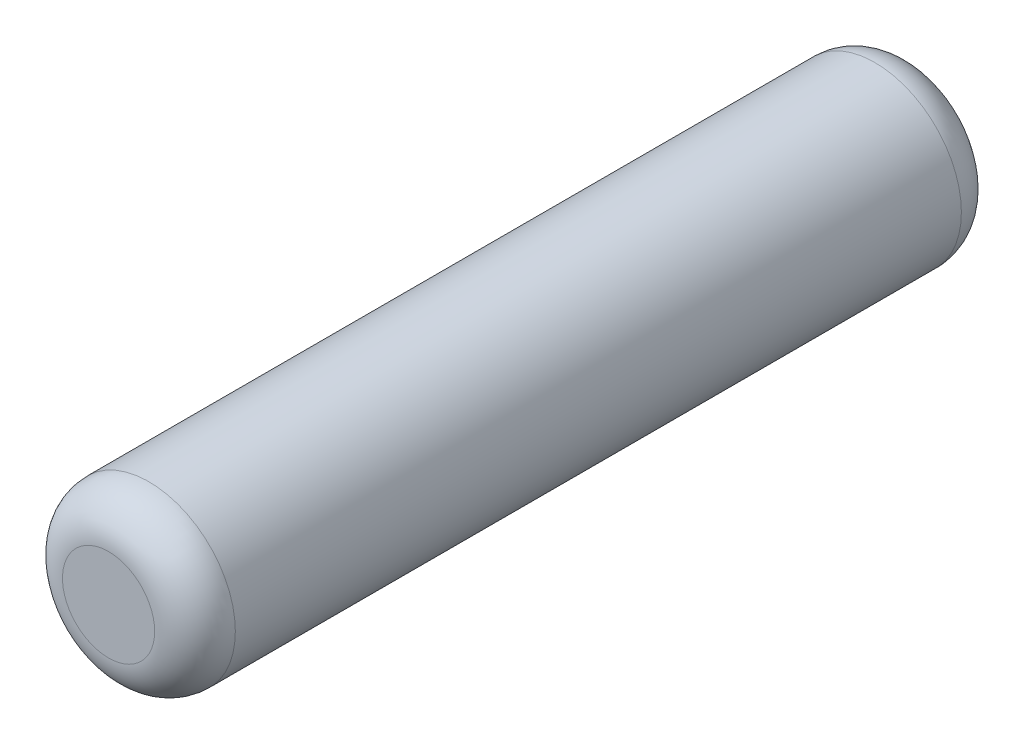
SolidWorks part; units mm, degrees
ref_plane "Front" through (0, 0, 0) normal (0, 0, 1) x (1, 0, 0)
ref_plane "Top" through (0, 0, 0) normal (0, 1, 0) x (1, 0, 0)
ref_plane "Right" through (0, 0, 0) normal (1, 0, 0) x (0, 0, -1)
sketch "Sketch1" plane through (0, 0, 0) normal (0, 0, 1) x (1, 0, 0)
  circle A0 centre (0, 0) radius 0.75
  dimension "D1" = 1.5
extrude "Boss-Extrude1" add sketch "Sketch1" along normal mid plane 7
fillet "Fillet1" radius 0.35 2 edges at (0.75, 0, -3.5) (0.75, 0, 3.5)
